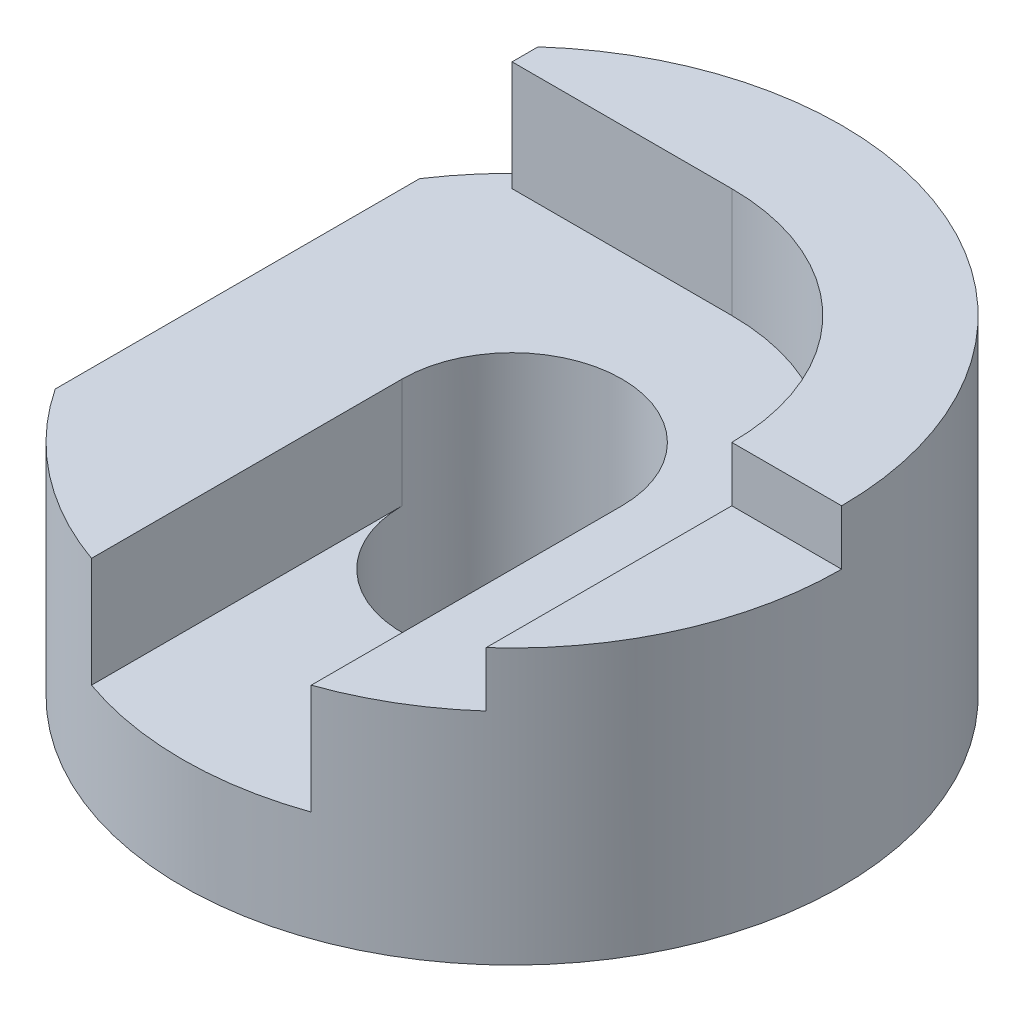
SolidWorks part; units mm, degrees
ref_plane "Front Plane" through (0, 0, 0) normal (0, 0, 1) x (1, 0, 0)
ref_plane "Top Plane" through (0, 0, 0) normal (0, 1, 0) x (1, 0, 0)
ref_plane "Right Plane" through (0, 0, 0) normal (1, 0, 0) x (0, 0, -1)
sketch "Sketch1" plane through (0, 0, 0) normal (0, 0, 1) x (1, 0, 0)
  line L1 (0, 0) -> (120, 0)
  line L2 (0, 0) -> (0, 60)
  line L3 (0, 60) -> (120, 60)
  line L4 (120, 0) -> (120, 60)
  dimension "D1" = 120
  dimension "D2" = 60
extrude "Boss-Extrude1" add sketch "Sketch1" along normal blind 120
sketch "Sketch2" plane through (0, 0, 120) normal (0, 0, 1) x (1, 0, 0)
  line L1 (0, 60) -> (10, 60)
  line L2 (0, 60) -> (0, 30)
  line L3 (0, 30) -> (10, 30)
  line L4 (10, 60) -> (10, 30)
  dimension "D1" = 10
  dimension "D2" = 30
extrude "Cut-Extrude1" cut sketch "Sketch2" against normal blind 120
sketch "Sketch3" plane through (0, 0, 120) normal (0, 0, 1) x (1, 0, 0)
  line L1 (10, 60) -> (20, 60)
  line L2 (10, 60) -> (10, 40)
  line L3 (10, 40) -> (20, 40)
  line L4 (20, 60) -> (20, 40)
  dimension "D1" = 10
  dimension "D2" = 20
extrude "Cut-Extrude2" cut sketch "Sketch3" against normal blind 120
sketch "Sketch5" plane through (0, 0, 0) normal (0, -1, 0) x (1, 0, 0)
  line L0 (0, 120) -> (0, 0)
  line L1 (0, 0) -> (120, 0)
  line L2 (120, 0) -> (120, 120)
  line L3 (120, 120) -> (0, 120)
  circle A0 centre (60, 60) radius 60
  line M1 (0, 0) -> (120, 0)
  line M2 (120, 0) -> (120, 120)
  line M3 (120, 120) -> (0, 120)
  line M4 (0, 120) -> (0, 0)
  dimension "D1" = 120
  dimension "D2" = 60
  dimension "D3" = 60
extrude "Cut-Extrude3" cut sketch "Sketch5" against normal blind 120 contours A0 L3 M4 | A0 L2 M3 | A0 L1 M2 | A0 L0 M1
sketch "Sketch6" plane through (0, 0, 0) normal (0, -1, 0) x (-1, 0, 0)
  circle A0 centre (-60, -60) radius 20
  circle A1 centre (-60, -60) radius 60 construction
  dimension "D1" = 40
  dimension "D2" = 0
extrude "Cut-Extrude4" cut sketch "Sketch6" against normal blind 120
sketch "Sketch7" plane through (0, 60, 0) normal (0, 1, 0) x (1, 0, 0)
  line L0 (40, -60) -> (40, -116.5685)
  line L1 (80, -60) -> (80, -116.5685)
  circle A0 centre (60, -60) radius 20 construction
  arc A1 (20, -104.7214) -> (20, -15.2786) centre (60, -60) ccw construction
  arc A2 (40, -60) -> (80, -60) centre (60, -60) ccw
  arc A3 (40, -116.5685) -> (80, -116.5685) centre (60, -60) ccw
  dimension "D1" = 40
extrude "Cut-Extrude5" cut sketch "Sketch7" against normal blind 20
sketch "Sketch8" plane through (0, 60, 0) normal (0, 1, 0) x (1, 0, 0)
  line L0 (60, -20) -> (20, -20)
  line L2 (20, -20) -> (20, -15.2786)
  line L3 (100, -60) -> (100, -104.7214)
  line L4 (100, -60) -> (120, -60)
  arc A0 (100, -60) -> (60, -20) centre (60, -60) ccw
  arc A1 (80, -116.5685) -> (20, -15.2786) centre (60, -60) ccw construction
  arc M1 (40, -60) -> (80, -60) centre (60, -60) cw
  line M2 (80, -60) -> (80, -116.5685)
  arc M3 (80, -116.5685) -> (20, -15.2786) centre (60, -60) ccw
  line M4 (20, -15.2786) -> (20, -104.7214)
  arc M5 (20, -104.7214) -> (40, -116.5685) centre (60, -60) ccw
  line M6 (40, -116.5685) -> (40, -60)
  dimension "D1" = 40
  dimension "D2" = 40
extrude "Cut-Extrude8" cut sketch "Sketch8" against normal blind 20 contours L3 A0 L0 M4 M5 M6 M1 M2 M3
sketch "Sketch9" plane through (100, 0, 0) normal (-1, 0, 0) x (0, 0, 1)
  line L1 (104.7214, 60) -> (89.7214, 60)
  line L2 (104.7214, 60) -> (104.7214, 50)
  line L3 (104.7214, 50) -> (89.7214, 50)
  line L4 (89.7214, 60) -> (89.7214, 50)
  dimension "D1" = 15
  dimension "D2" = 10
extrude "Cut-Extrude10" cut sketch "Sketch9" against normal blind 20
sketch "Sketch10" plane through (100, 0, 0) normal (-1, 0, 0) x (0, 0, 1)
  line L1 (60, 60) -> (89.7214, 60)
  line L2 (60, 60) -> (60, 50)
  line L3 (60, 50) -> (89.7214, 50)
  line L4 (89.7214, 60) -> (89.7214, 50)
extrude "Cut-Extrude11" cut sketch "Sketch10" against normal blind 20
sketch "Sketch11" plane through (0, 40, 0) normal (0, 1, 0) x (1, 0, 0)
  line L0 (40, -60) -> (40, -116.5685)
  line L1 (80, -60) -> (80, -116.5685)
  circle A0 centre (60, -60) radius 20 construction
  arc A1 (10, -93.1662) -> (100, -104.7214) centre (60, -60) ccw construction
  arc A2 (40, -60) -> (80, -60) centre (60, -60) ccw
  arc A3 (40, -116.5685) -> (80, -116.5685) centre (60, -60) ccw
  dimension "D1" = 40
extrude "Cut-Extrude12" cut sketch "Sketch11" against normal blind 20
sketch "Sketch12" plane through (40, 0, 0) normal (1, 0, 0) x (0, 0, -1)
  line L0 (-60, 40) -> (-116.5685, 40) construction
  line L1 (-40, 20) -> (-80, 20)
  line L2 (-40, 20) -> (-40, 40)
  line L3 (-40, 40) -> (-80, 40)
  line L4 (-80, 20) -> (-80, 40)
  dimension "D1" = 40
  dimension "D2" = 40
  dimension "D3" = 20
extrude "Cut-Extrude15" cut sketch "Sketch12" against normal blind 20
sketch "Sketch14" plane through (0, 40, 0) normal (0, 1, 0) x (1, 0, 0)
  line L1 (20, -40) -> (40, -40)
  line L2 (20, -40) -> (20, -80)
  line L3 (20, -80) -> (40, -80)
  line L4 (40, -40) -> (40, -80)
extrude "Boss-Extrude6" add sketch "Sketch14" against normal blind 20
